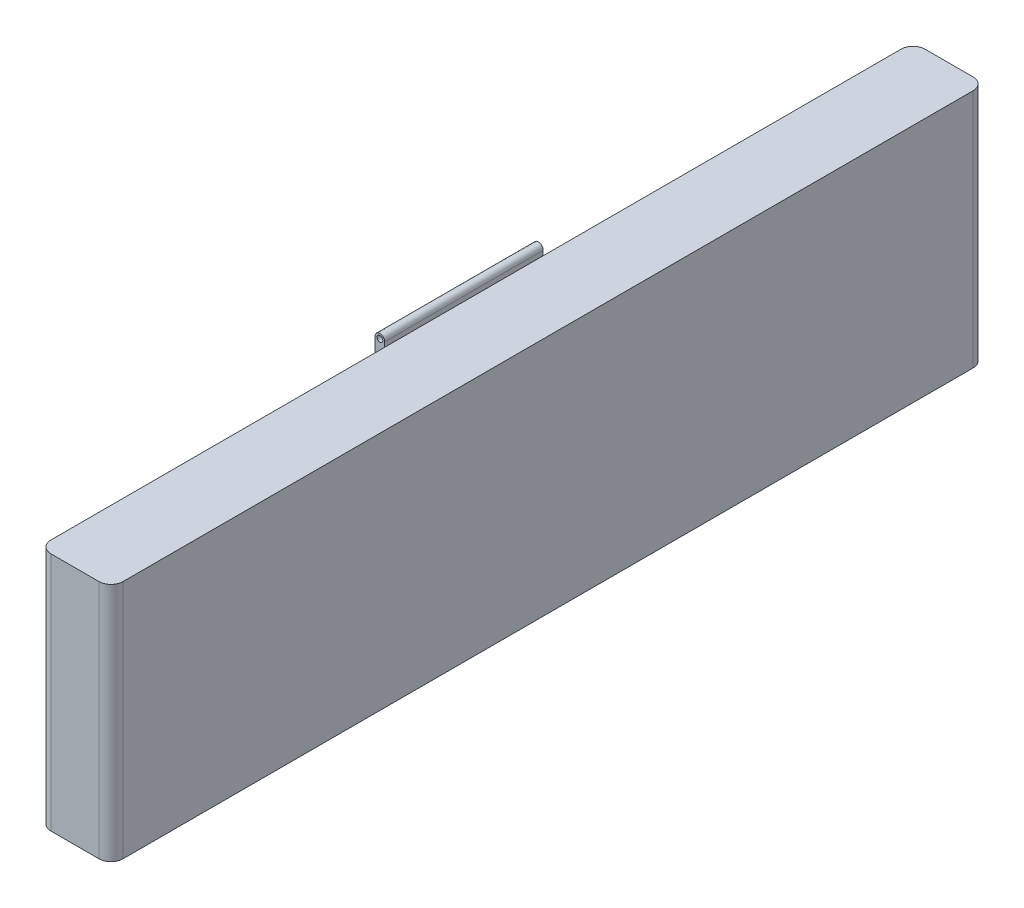
SolidWorks part; units mm, degrees
ref_plane "Front Plane" through (0, 0, 0) normal (0, 0, 1) x (1, 0, 0)
ref_plane "Top Plane" through (0, 0, 0) normal (0, 1, 0) x (1, 0, 0)
ref_plane "Right Plane" through (0, 0, 0) normal (1, 0, 0) x (0, 0, -1)
sketch "Sketch2" plane through (0, 0, 0) normal (1, 0, 0) x (0, 0, -1)
  line L0 (0, 0) -> (0, 5)
  line L1 (0, 5) -> (-18.2, 5)
  line L2 (-18.2, 5) -> (-18.2, 0)
  line L3 (-18.2, 0) -> (0, 0)
  dimension "D1" = 18.2
  dimension "D2" = 5
extrude "Boss-Extrude1" add sketch "Sketch2" along normal blind 1.5
ref_plane "Plane1" through (0, 0, 11) normal (0, 0, 1) x (1, 0, 0)
sketch "Sketch3" plane through (0, 0, 11) normal (0, 0, 1) x (1, 0, 0)
  line L0 (0, 2.5) -> (-2.7079, 2.5) construction
  line L1 (0, 5) -> (0, 0) construction
  line L2 (0, 2.5) -> (0, 3.1)
  line L3 (0, 3.1) -> (-0.3, 3.1)
  line L4 (-0.3, 3.1) -> (-0.3, 2.8)
  line L5 (-0.3, 2.8) -> (-0.6, 2.8)
  line L6 (-0.6, 2.8) -> (-0.6, 2.5)
  line L7 (-0.6, 2.5) -> (0, 2.5)
  dimension "D3" = 0.3
  dimension "D4" = 0.6
  dimension "D1" = 0.6
  dimension "D2" = 0.3
revolve "Revolve1" add sketch "Sketch3" angle 360 about L0
sketch "Sketch4" plane through (0, 0, 0) normal (-1, 0, 0) x (0, 0, 1)
  line L0 (9.5, 2.2) -> (9.5, 2.8)
  line L1 (9.5, 2.8) -> (5.9, 2.8)
  line L2 (5.9, 2.8) -> (5.9, 2.2)
  line L3 (5.9, 2.2) -> (9.5, 2.2)
  line L4 (18.2, 5) -> (18.2, 0) construction
  circle A0 centre (11, 2.5) radius 0.3 construction
  point P4 (9.5, 2.5)
  point P7 (18.2, 2.5)
  dimension "D1" = 0.6
  dimension "D2" = 3.6
  dimension "D3" = 1.5
extrude "Cut-Extrude1" cut sketch "Sketch4" against normal blind 0.6 contours L1 L2 L3 L0
sketch "Sketch5" plane through (0, 0, 0) normal (-1, 0, 0) x (0, 0, 1)
  line L0 (11, 5.1) -> (11, 4.6)
  line L2 (11, 4.6) -> (7.7, 4.6)
  line L3 (7.7, 4.6) -> (7.7, 5.1)
  line L4 (7.7, 5.1) -> (11, 5.1)
  line L5 (9.5, 2.8) -> (5.9, 2.8) construction
  point P18 (7.7, 2.8)
  dimension "D1" = 0.5
  dimension "D2" = 0.4
extrude "Boss-Extrude2" add sketch "Sketch5" along normal blind 0.2
sketch "Sketch6" plane through (0, 0, 11) normal (0, 0, 1) x (1, 0, 0)
  line L1 (-0.2, 4.9359) -> (-0.2, 5.1506) construction
  line L2 (-0.2, 4.6) -> (-0.2, 5.1) construction
  line L4 (-0.2, 5.1) -> (0, 5.1)
  arc A0 (-0.2, 5.1) -> (0, 5.1) centre (-0.1, 5.1) cw
extrude "Boss-Extrude5" add sketch "Sketch6" against normal up to surface (3.3 mm away) contours A0 L4 up to face at (-0.08, 4.88, 7.7)
sketch "Sketch9" plane through (0, 0, 11) normal (0, 0, 1) x (1, 0, 0)
  circle A0 centre (-0.1, 5.1) radius 0.06
  dimension "D1" = 0.12
extrude "Cut-Extrude5" cut sketch "Sketch9" against normal through all
ref_plane "Plane2" through (0, 2.5, 0) normal (0, 1, 0) x (1, 0, 0)
mirror "Mirror8" about plane through (0, 2.5, 0) normal (0, 1, 0) of "Cut-Extrude5", "Boss-Extrude2", "Boss-Extrude5"
fillet "Fillet1" radius 0.25 4 edges at (0, 2.5, 0) (1.5, 2.5, 0) (0, 2.5, 18.2) (1.5, 2.5, 18.2)
equation "\"Connector Depth\"=0.6"
equation "\"D4@Sketch3\"=\"Connector Depth\""
equation "\"D3@Sketch3\"=\"Connector Depth\"/2"
equation "\"D1@Sketch3\"=\"Connector Depth\""
equation "\"D2@Sketch3\"=\"Connector Depth\"/2"
equation "\"D1@Sketch4\"=\"Connector Depth\""
equation "\"D2@Sketch4\"=\"Connector Depth\"*6"
equation "\"D1@Cut-Extrude1\"=\"Connector Depth\""
